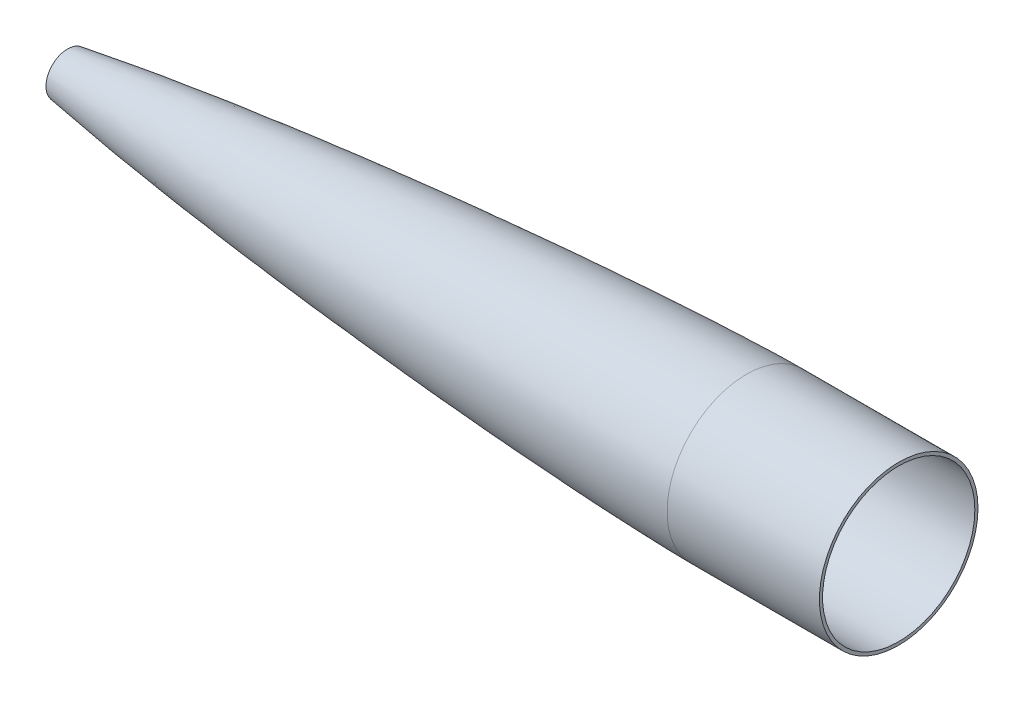
SolidWorks part; units mm, degrees
material "S-Glass Fiber"
ref_plane "Front Plane" through (0, 0, 0) normal (0, 0, 1) x (1, 0, 0)
ref_plane "Top Plane" through (0, 0, 0) normal (0, 1, 0) x (1, 0, 0)
ref_plane "Right Plane" through (0, 0, 0) normal (1, 0, 0) x (0, 0, -1)
sketch "Sketch1" plane through (0, 0, 0) normal (0, 0, 1) x (1, 0, 0)
  line L0 (762, 76.2) -> (914.4, 76.2)
  line L1 (914.4, 76.2) -> (914.4, 79.375)
  line L2 (914.4, 79.375) -> (762, 79.375)
  line L3 (993.4698, 0) -> (0, 0) construction
  line L5 (82.55, 21.6094) -> (82.55, 18.4344)
  spline S0 degree 4 poles (15.9643, 5.4501) (16.5964, 5.6111) (17.8617, 5.9295) (20.7066, 6.6268) (25.6938, 7.7907) (31.4913, 9.0612) (38.0572, 10.4226) (44.9925, 11.7947) (51.6189, 13.0579) (58.193, 14.2624) (64.3789, 15.3634) (70.2369, 16.3761) (74.7925, 17.152) (80.6718, 18.1286) (84.6429, 18.7778) (90.7444, 19.7605) (95.4345, 20.4978) (100.9787, 21.3612) (106.0589, 22.136) (112.6869, 23.1348) (121.5881, 24.4482) (132.9609, 26.0828) (148.2286, 28.2049) (163.5411, 30.2533) (177.7572, 32.0934) (193.5363, 34.0795) (209.3158, 36.0118) (227.7381, 38.195) (248.8, 40.599) (269.8729, 42.9184) (290.9536, 45.1578) (312.0427, 47.3214) (333.1389, 49.4121) (354.242, 51.4325) (375.3515, 53.3846) (396.4672, 55.2699) (417.5885, 57.0895) (443.9971, 59.2827) (475.698, 61.7851) (512.6968, 64.5153) (555.0001, 67.3694) (597.3214, 69.9425) (639.6603, 72.2102) (678.4358, 73.967) (711.7231, 75.179) (735.7209, 75.822) (749.7734, 76.0837) (757.4607, 76.1732) (760.0546, 76.1932) (761.3515, 76.1986) (762, 76.2) knots 0 0 0 0 0 0.00348 0.006961 0.015602 0.027337 0.035068 0.042798 0.05317 0.063541 0.070269 0.076998 0.083726 0.090454 0.097519 0.104583 0.111648 0.118713 0.125777 0.132842 0.146971 0.166926 0.186881 0.21514 0.229269 0.243398 0.271657 0.299915 0.328174 0.356432 0.384691 0.41295 0.441208 0.469467 0.497725 0.525984 0.554242 0.582501 0.639018 0.695535 0.752052 0.808569 0.865086 0.921604 0.959009 0.986169 0.993085 0.996542 1 1 1 1 1 construction
  spline S1 degree 4 poles (82.55, 18.4344) (83.7393, 18.6289) (86.1131, 19.0146) (90.7444, 19.7605) (95.4345, 20.4978) (100.9787, 21.3612) (106.0589, 22.136) (112.6869, 23.1348) (121.5881, 24.4482) (132.9609, 26.0828) (148.2286, 28.2049) (163.5411, 30.2533) (177.7572, 32.0934) (193.5363, 34.0795) (209.3158, 36.0118) (227.7381, 38.195) (248.8, 40.599) (269.8729, 42.9184) (290.9536, 45.1578) (312.0427, 47.3214) (333.1389, 49.4121) (354.242, 51.4325) (375.3515, 53.3846) (396.4672, 55.2699) (417.5885, 57.0895) (443.9971, 59.2827) (475.698, 61.7851) (512.6968, 64.5153) (555.0001, 67.3694) (597.3214, 69.9425) (639.6603, 72.2102) (678.4358, 73.967) (711.7231, 75.179) (735.7209, 75.822) (749.7734, 76.0837) (757.4607, 76.1732) (760.0546, 76.1932) (761.3515, 76.1986) (762, 76.2) knots 0.090454 0.090454 0.090454 0.090454 0.090454 0.097519 0.104583 0.111648 0.118713 0.125777 0.132842 0.146971 0.166926 0.186881 0.21514 0.229269 0.243398 0.271657 0.299915 0.328174 0.356432 0.384691 0.41295 0.441208 0.469467 0.497725 0.525984 0.554242 0.582501 0.639018 0.695535 0.752052 0.808569 0.865086 0.921604 0.959009 0.986169 0.993085 0.996542 1 1 1 1 1
  spline S2 degree 4 poles (15.9643, 8.6251) (16.5964, 8.7861) (17.8617, 9.1045) (20.7066, 9.8018) (25.6938, 10.9657) (31.4913, 12.2362) (38.0572, 13.5976) (44.9925, 14.9697) (51.6189, 16.2329) (58.193, 17.4374) (64.3789, 18.5384) (70.2369, 19.5511) (74.7925, 20.327) (80.6718, 21.3036) (84.6429, 21.9528) (90.7444, 22.9355) (95.4345, 23.6728) (100.9787, 24.5362) (106.0589, 25.311) (112.6869, 26.3098) (121.5881, 27.6232) (132.9609, 29.2578) (148.2286, 31.3799) (163.5411, 33.4283) (177.7572, 35.2684) (193.5363, 37.2545) (209.3158, 39.1868) (227.7381, 41.37) (248.8, 43.774) (269.8729, 46.0934) (290.9536, 48.3328) (312.0427, 50.4964) (333.1389, 52.5871) (354.242, 54.6075) (375.3515, 56.5596) (396.4672, 58.4449) (417.5885, 60.2645) (443.9971, 62.4577) (475.698, 64.9601) (512.6968, 67.6903) (555.0001, 70.5444) (597.3214, 73.1175) (639.6603, 75.3852) (678.4358, 77.142) (711.7231, 78.354) (735.7209, 78.997) (749.7734, 79.2587) (757.4607, 79.3482) (760.0546, 79.3682) (761.3515, 79.3736) (762, 79.375) knots 0 0 0 0 0 0.00348 0.006961 0.015602 0.027337 0.035068 0.042798 0.05317 0.063541 0.070269 0.076998 0.083726 0.090454 0.097519 0.104583 0.111648 0.118713 0.125777 0.132842 0.146971 0.166926 0.186881 0.21514 0.229269 0.243398 0.271657 0.299915 0.328174 0.356432 0.384691 0.41295 0.441208 0.469467 0.497725 0.525984 0.554242 0.582501 0.639018 0.695535 0.752052 0.808569 0.865086 0.921604 0.959009 0.986169 0.993085 0.996542 1 1 1 1 1 construction
  spline S3 degree 4 poles (82.55, 21.6094) (83.7393, 21.8039) (86.1131, 22.1896) (90.7444, 22.9355) (95.4345, 23.6728) (100.9787, 24.5362) (106.0589, 25.311) (112.6869, 26.3098) (121.5881, 27.6232) (132.9609, 29.2578) (148.2286, 31.3799) (163.5411, 33.4283) (177.7572, 35.2684) (193.5363, 37.2545) (209.3158, 39.1868) (227.7381, 41.37) (248.8, 43.774) (269.8729, 46.0934) (290.9536, 48.3328) (312.0427, 50.4964) (333.1389, 52.5871) (354.242, 54.6075) (375.3515, 56.5596) (396.4672, 58.4449) (417.5885, 60.2645) (443.9971, 62.4577) (475.698, 64.9601) (512.6968, 67.6903) (555.0001, 70.5444) (597.3214, 73.1175) (639.6603, 75.3852) (678.4358, 77.142) (711.7231, 78.354) (735.7209, 78.997) (749.7734, 79.2587) (757.4607, 79.3482) (760.0546, 79.3682) (761.3515, 79.3736) (762, 79.375) knots 0.090454 0.090454 0.090454 0.090454 0.090454 0.097519 0.104583 0.111648 0.118713 0.125777 0.132842 0.146971 0.166926 0.186881 0.21514 0.229269 0.243398 0.271657 0.299915 0.328174 0.356432 0.384691 0.41295 0.441208 0.469467 0.497725 0.525984 0.554242 0.582501 0.639018 0.695535 0.752052 0.808569 0.865086 0.921604 0.959009 0.986169 0.993085 0.996542 1 1 1 1 1
  dimension "D1" = 76.2
  dimension "6" = 152.4
  dimension "D2" = 3.175
  dimension "D3" = 914.4
revolve "Revolve1" add sketch "Sketch1" angle 360 about L3
